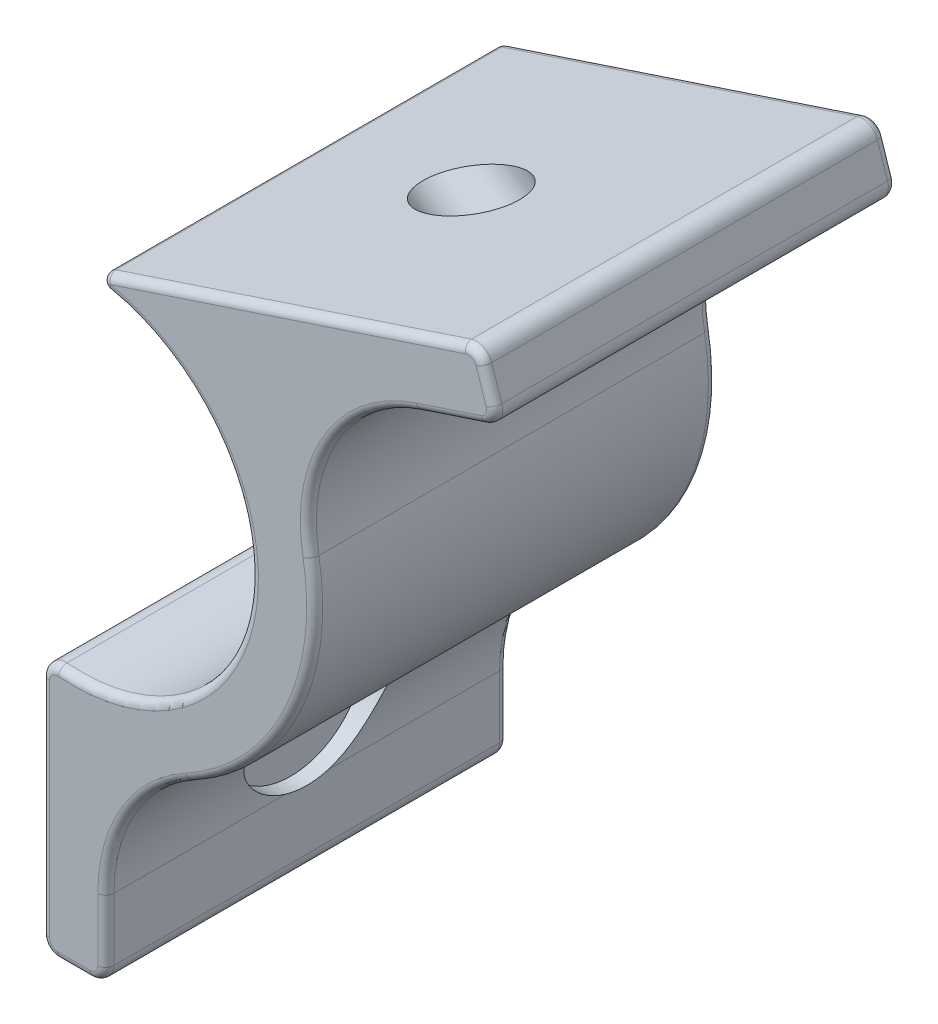
SolidWorks part; units mm, degrees
ref_plane "Ön Düzlem" through (0, 0, 0) normal (0, 0, 1) x (1, 0, 0)
ref_plane "Üst Düzlem" through (0, 0, 0) normal (0, 1, 0) x (1, 0, 0)
ref_plane "Sağ Düzlem" through (0, 0, 0) normal (1, 0, 0) x (0, 0, -1)
sketch "Çizim1" plane through (0, 0, 0) normal (0, 0, 1) x (1, 0, 0)
  line L0 (6.5163, -38.0832) -> (6.5163, -24.2241)
  line L1 (10.6451, -0.5215) -> (32.7637, 6.8003)
  line L2 (10.5163, -38.0832) -> (10.5163, -34.1929)
  line L3 (29.9701, 1.6621) -> (34.0207, 3.003)
  line L4 (10.5163, -39.0832) -> (10.5163, -27.1303) construction
  line L5 (19.3173, -1.8642) -> (34.97, 3.3173) construction
  line L6 (7.5163, -39.0832) -> (9.5163, -39.0832)
  line L7 (34.0273, 6.1653) -> (34.6558, 4.2666)
  line L8 (8.3968, -1.2658) -> (33.713, 7.1146) construction
  line L9 (6.5163, -39.0832) -> (6.5163, -23.0832) construction
  arc A0 (7.599, -23.2275) -> (10.7025, -1.4861) centre (8.509, -12.2652) ccw
  arc A1 (15.7134, -25.4218) -> (23.2712, -9.6048) centre (8.509, -12.2652) ccw
  arc A2 (10.5163, -27.1303) -> (19.3173, -1.8642) centre (8.509, -12.2652) ccw construction
  arc A3 (10.5163, -34.1929) -> (15.7134, -25.4218) centre (20.5163, -34.1929) cw
  arc A4 (23.2712, -9.6048) -> (29.9701, 1.6621) centre (33.1126, -7.8313) cw
  arc A5 (6.5163, -23.0832) -> (8.3968, -1.2658) centre (8.509, -12.2652) ccw construction
  arc A6 (10.6451, -0.5215) -> (10.7025, -1.4861) centre (10.8023, -0.9962) ccw
  arc A7 (34.0207, 3.003) -> (34.6558, 4.2666) centre (33.7064, 3.9523) ccw
  arc A8 (32.7637, 6.8003) -> (34.0273, 6.1653) centre (33.0779, 5.851) cw
  arc A9 (10.5163, -38.0832) -> (9.5163, -39.0832) centre (9.5163, -38.0832) cw
  arc A10 (6.5163, -38.0832) -> (7.5163, -39.0832) centre (7.5163, -38.0832) ccw
  arc A11 (7.599, -23.2275) -> (6.5163, -24.2241) centre (7.5163, -24.2241) ccw
  point P23 (8.3968, -1.2658)
  point P36 (6.5163, -39.0832)
  dimension "D2" = 10
  dimension "D3" = 0.5
  dimension "D4" = 1
  dimension "D1" = 4
extrude "Yükseklik-Ekstrüzyon1" add sketch "Çizim1" against normal blind 25
ref_plane "Düzlem1" through (15.5163, 0, 0) normal (1, 0, 0) x (0, 0, -1)
sketch "Çizim4" plane through (15.5163, 0, 0) normal (1, 0, 0) x (0, 0, -1)
  line L1 (-2, -29.7832) -> (25, -29.7832) construction
  line L3 (25, -34.1929) -> (25, -25.4218) construction
  line L4 (25, -39.0832) -> (0, -39.0832) construction
  circle A0 centre (12.5, -29.7832) radius 2.6
  dimension "D1" = 9.3
  dimension "D2" = 12.5
extrude "Kes-Ekstrüzyon1" cut sketch "Çizim4" against normal up to surface (9 mm away) up to face at (6.5163, -31.1536, -12.5)
sketch "Çizim5" plane through (15.5163, 0, 0) normal (1, 0, 0) x (0, 0, -1)
  circle A0 centre (12.5, -29.7832) radius 4.6
extrude "Kes-Ekstrüzyon2" cut sketch "Çizim5" against normal blind 6
ref_plane "Düzlem2" through (20.4404, -15.227, 0) normal (0.8019, -0.5974, 0) x (0, 0, 1)
sketch "Çizim6" plane through (20.4404, -15.227, 0) normal (0.8019, -0.5974, 0) x (0, 0, 1)
  line L0 (-25, -14.6659) -> (0, -14.6659) construction
  line L1 (-25, -6.1997) -> (-25, -19.2371) construction
  line L2 (0, -19.2371) -> (0, -6.1997) construction
  circle A0 centre (-12.5, -14.6659) radius 2.6
  dimension "D1" = 12.5
extrude "Kes-Ekstrüzyon3" cut sketch "Çizim6" against normal blind 36.5 contours A0
sketch "Çizim7" plane through (20.4404, -15.227, 0) normal (0.8019, -0.5974, 0) x (0, 0, 1)
  circle A0 centre (-12.5, -14.6659) radius 4.6
extrude "Kes-Ekstrüzyon4" cut sketch "Çizim7" against normal blind 5
fillet "Radyus1" radius 0.5 32 edges at (22.0433, -18.7323, -25) (24.5172, -2.7207, -25) (31.9954, 2.3326, -25) (34.5999, 3.5033, -25) (34.3415, 5.2159, -25) (33.527, 6.7445, -25) (21.7044, 3.1394, -25) (10.3031, -1.0259, -25) (19.3986, -13.8197, -25) (6.8391, -23.4883, -25) (6.5163, -31.1536, -25) (6.8092, -38.7903, -25) (8.5163, -39.0832, -25) (10.2234, -38.7903, -25) (10.5163, -36.1381, -25) (11.9131, -29.0953, -25) (10.5163, -36.1381, 0) (10.2234, -38.7903, 0) (8.5163, -39.0832, 0) (6.8092, -38.7903, 0) (6.5163, -31.1536, 0) (6.8391, -23.4883, 0) (19.3986, -13.8197, 0) (10.3031, -1.0259, 0) (21.7044, 3.1394, 0) (33.527, 6.7445, 0) (34.3415, 5.2159, 0) (34.5999, 3.5033, 0) (31.9954, 2.3326, 0) (24.5172, -2.7207, 0) (22.0433, -18.7323, 0) (11.9131, -29.0953, 0)
